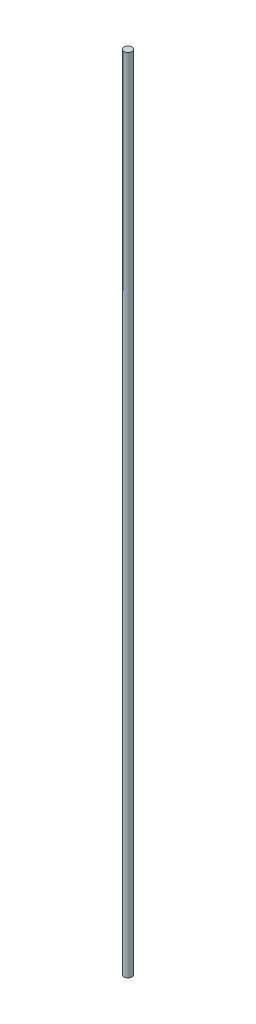
SolidWorks part; units mm, degrees
ref_plane "Plan de face" through (0, 0, 0) normal (0, 0, 1) x (1, 0, 0)
ref_plane "Plan de dessus" through (0, 0, 0) normal (0, 1, 0) x (1, 0, 0)
ref_plane "Plan de droite" through (0, 0, 0) normal (1, 0, 0) x (0, 0, -1)
sketch "Esquisse1" plane through (0, 0, 0) normal (0, 1, 0) x (1, 0, 0)
  circle A0 centre (0, 0) radius 1.5
  dimension "D1" = 3
extrude "Boss.-Extru.1" add sketch "Esquisse1" along normal blind 300
